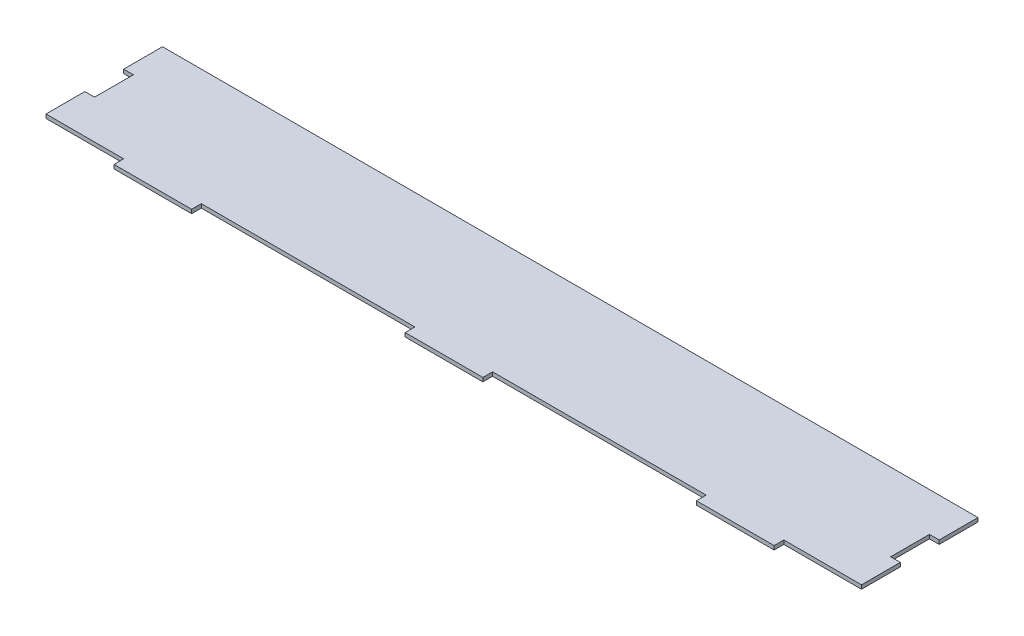
SolidWorks part; units mm, degrees
ref_plane "Front Plane" through (0, 0, 0) normal (0, 0, 1) x (1, 0, 0)
ref_plane "Top Plane" through (0, 0, 0) normal (0, 1, 0) x (1, 0, 0)
ref_plane "Right Plane" through (0, 0, 0) normal (1, 0, 0) x (0, 0, -1)
sketch "Sketch1" plane through (0, 0, 0) normal (0, 1, 0) x (1, 0, 0)
  line L0 (0, -25.4) -> (0, 0)
  line L1 (0, 0) -> (533.4, 0)
  line L2 (0, -50.8) -> (0, -76.2)
  line L3 (0, -76.2) -> (50.8, -76.2)
  line L4 (533.4, 0) -> (533.4, -25.4)
  line L5 (0, -25.4) -> (6.35, -25.4)
  line L6 (533.4, -50.8) -> (533.4, -76.2)
  line L7 (0, -50.8) -> (6.35, -50.8)
  line L8 (6.35, -25.4) -> (6.35, -50.8)
  line L9 (533.4, 0) -> (527.05, 0)
  line L10 (533.4, -25.4) -> (527.05, -25.4)
  line L11 (101.6, -76.2) -> (241.3, -76.2)
  line L12 (533.4, -50.8) -> (527.05, -50.8)
  line L13 (482.6, -76.2) -> (533.4, -76.2)
  line L14 (527.05, -25.4) -> (527.05, -50.8)
  line L15 (292.1, -76.2) -> (431.8, -76.2)
  line L16 (50.8, -76.2) -> (50.8, -82.55)
  line L17 (50.8, -82.55) -> (101.6, -82.55)
  line L18 (101.6, -76.2) -> (101.6, -82.55)
  line L20 (482.6, -76.2) -> (482.6, -82.55)
  line L21 (482.6, -82.55) -> (431.8, -82.55)
  line L22 (431.8, -76.2) -> (431.8, -82.55)
  line L24 (241.3, -76.2) -> (241.3, -82.55)
  line L25 (241.3, -82.55) -> (292.1, -82.55)
  line L26 (292.1, -76.2) -> (292.1, -82.55)
  dimension "D1" = 76.2
  dimension "D2" = 533.4
  dimension "D3" = 6.35
  dimension "D4" = 25.4
  dimension "D5" = 50.8
  dimension "D6" = 6.35
  dimension "D7" = 25.4
  dimension "D8" = 25.4
  dimension "D9" = 25.4
  dimension "D10" = 25.4
  dimension "D11" = 25.4
  dimension "D12" = 6.35
  dimension "D13" = 50.8
  dimension "D14" = 50.8
  dimension "D15" = 6.35
  dimension "D16" = 533.4
  dimension "D17" = 6.35
  dimension "D18" = 50.8
  dimension "D19" = 50.8
  dimension "D20" = 50.8
  dimension "D21" = 6.35
  dimension "D22" = 139.7
  dimension "D23" = 139.7
  dimension "D24" = 139.7
  dimension "D25" = 139.7
  dimension "D26" = 50.8
  dimension "D27" = 6.35
  dimension "D28" = 6.35
  dimension "D29" = 6.35
  dimension "D30" = 25.4
  dimension "D31" = 25.4
  dimension "D32" = 25.4
extrude "Boss-Extrude1" add sketch "Sketch1" along normal blind 2.54 contours L26 L15 L22 L21 L20 L13 L6 L12 L14 L10 L4 L1 L0 L5 L8 L7 L2 L3 L16 L17 L18 L11 L24 L25
